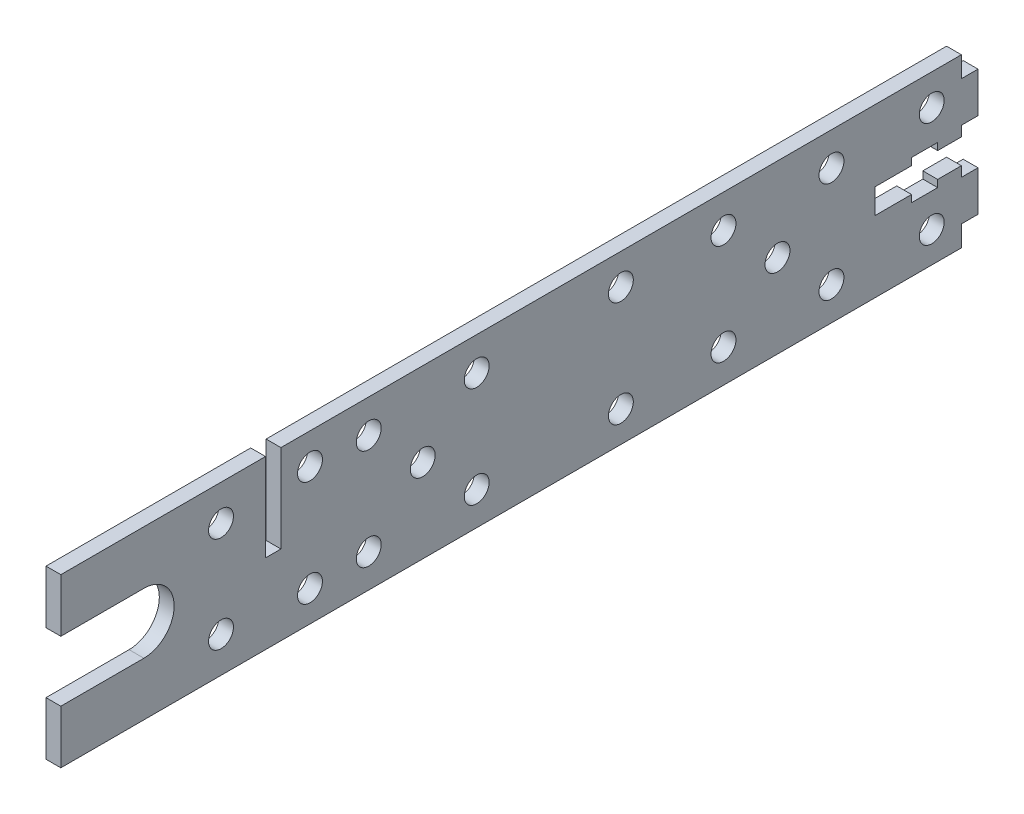
SolidWorks part; units mm, degrees
ref_plane "Front Plane" through (0, 0, 0) normal (0, 0, 1) x (1, 0, 0)
ref_plane "Top Plane" through (0, 0, 0) normal (0, 1, 0) x (1, 0, 0)
ref_plane "Right Plane" through (0, 0, 0) normal (1, 0, 0) x (0, 0, -1)
sketch "Sketch1" plane through (0, 0, 0) normal (1, 0, 0) x (0, 0, -1)
  line L0 (-98.171, 0) -> (98.171, 0) construction
  line L1 (-98.171, 17.907) -> (94.615, 17.907)
  line L2 (-98.171, 17.907) -> (-98.171, 6.477)
  line L3 (-98.171, -17.907) -> (94.615, -17.907)
  line L4 (98.171, 13.462) -> (98.171, 4.826)
  line L5 (94.615, 4.826) -> (94.615, 2.667)
  line L6 (94.615, -2.667) -> (94.615, -4.826)
  line L7 (94.615, 2.667) -> (89.535, 2.667)
  line L8 (94.615, 17.907) -> (94.615, 13.462)
  line L9 (94.615, -2.667) -> (89.535, -2.667)
  line L10 (76.073, 2.667) -> (76.073, -2.667)
  line L11 (86.741, 4.191) -> (86.741, -4.191) construction
  line L12 (-32.258, 10.795) -> (-9.144, 10.795) construction
  line L13 (83.947, 2.667) -> (76.073, 2.667)
  line L14 (89.535, 4.191) -> (83.947, 4.191)
  line L15 (89.535, 4.191) -> (89.535, 2.667)
  line L16 (89.535, -4.191) -> (83.947, -4.191)
  line L17 (83.947, 4.191) -> (83.947, 2.667)
  line L18 (66.802, 10.795) -> (43.688, 10.795) construction
  line L19 (66.802, -10.795) -> (43.688, -10.795) construction
  line L20 (83.947, -2.667) -> (76.073, -2.667)
  line L21 (89.535, -2.667) -> (89.535, -4.191)
  line L22 (83.947, -2.667) -> (83.947, -4.191)
  line L23 (98.171, -4.826) -> (98.171, -13.462)
  line L24 (98.171, 13.462) -> (94.615, 13.462)
  line L25 (98.171, 13.462) -> (98.171, 4.826)
  line L26 (98.171, 4.826) -> (94.615, 4.826)
  line L27 (-32.258, -10.795) -> (-9.144, -10.795) construction
  line L28 (98.171, 13.462) -> (94.615, 4.826) construction
  line L29 (98.171, 4.826) -> (94.615, 13.462) construction
  line L30 (-80.391, 6.477) -> (-98.171, 6.477)
  line L31 (98.171, -4.826) -> (94.615, -4.826)
  line L32 (-20.701, 10.795) -> (-20.701, -10.795) construction
  line L33 (98.171, -13.462) -> (94.615, -4.826) construction
  line L34 (98.171, -4.826) -> (94.615, -13.462) construction
  line L35 (98.171, -13.462) -> (94.615, -13.462)
  line L36 (-80.391, -6.477) -> (-98.171, -6.477)
  line L37 (-98.171, -6.477) -> (-98.171, -17.907)
  line L38 (94.615, -13.462) -> (94.615, -17.907)
  line L39 (55.245, 10.795) -> (55.245, -10.795) construction
  arc A0 (-80.391, -6.477) -> (-80.391, 6.477) centre (-80.391, 0) ccw
  circle A1 centre (-63.881, 10.287) radius 2.667
  circle A2 centre (-63.881, -10.287) radius 2.667
  circle A3 centre (-52.705, 0) radius 2.667
  circle A4 centre (-44.831, 11.303) radius 2.667
  circle A5 centre (21.717, 11.303) radius 2.667
  circle A6 centre (88.265, 11.303) radius 2.667
  circle A7 centre (88.265, -11.303) radius 2.667
  circle A8 centre (21.717, -11.303) radius 2.667
  circle A9 centre (-44.831, -11.303) radius 2.667
  circle A10 centre (-9.144, 10.795) radius 2.667
  circle A11 centre (-32.258, 10.795) radius 2.667
  circle A12 centre (66.802, 10.795) radius 2.667
  circle A13 centre (43.688, 10.795) radius 2.667
  circle A14 centre (43.688, -10.795) radius 2.667
  circle A15 centre (66.802, -10.795) radius 2.667
  circle A16 centre (-32.258, -10.795) radius 2.667
  circle A17 centre (-9.144, -10.795) radius 2.667
  circle A18 centre (-20.701, 0) radius 2.667
  circle A19 centre (55.245, 0) radius 2.667
  point P0 (0, 0)
  point P1 (86.741, 0)
  point P4 (0, 0)
  point P26 (96.393, 9.144)
  point P30 (96.393, -9.144)
  point P44 (76.073, 0)
  point P63 (55.245, 10.795)
  point P73 (-20.701, 10.795)
  dimension "D11" = 12.954
  dimension "D15" = 5.334
  dimension "D26" = 17.78
  dimension "D2" = 192.786
  dimension "D3" = 5.334
  dimension "D4" = 18.542
  dimension "D5" = 5.588
  dimension "D6" = 8.636
  dimension "D7" = 8.382
  dimension "D8" = 3.556
  dimension "D9" = 8.636
  dimension "D10" = 9.144
  dimension "D12" = 17.78
  dimension "D13" = 11.43
  dimension "D14" = 11.43
  dimension "D16" = 7.62
  dimension "D17" = 34.29
  dimension "D18" = 150.876
  dimension "D19" = 9.906
  dimension "D20" = 6.604
  dimension "D21" = 76.454
  dimension "D22" = 143.002
  dimension "D23" = 7.112
  dimension "D24" = 42.926
  dimension "D25" = 118.872
extrude "Boss-Extrude1" add sketch "Sketch1" along normal mid plane 3.175 contours A0 L36 L37 L3 L6 L9 L21 L16 L22 L20 L10 L13 L17 L14 L15 L7 L5 L26 L4 L24 L8 L1 L2 L30 A16 A14 A13 A12 A11 A10 A8 A2 A1 A3 A4 A5 | A3
sketch "Sketch2" plane through (1.5875, 0, 0) normal (1, 0, 0) x (0, 0, -1)
  line L0 (-98.171, 17.907) -> (94.615, 17.907) construction
  line L1 (-54.356, 17.907) -> (-51.054, 17.907)
  line L2 (-54.356, 17.907) -> (-54.356, -0.889)
  line L3 (-54.356, -0.889) -> (-51.054, -0.889)
  line L4 (-51.054, 17.907) -> (-51.054, -0.889)
  line L5 (-54.356, 17.907) -> (-51.054, -0.889) construction
  line L6 (-54.356, -0.889) -> (-51.054, 17.907) construction
  line L7 (98.171, -4.826) -> (98.171, -13.462) construction
  point P4 (-52.705, 8.509)
  point P9 (98.171, -9.144)
  dimension "D1" = 3.302
  dimension "D2" = 18.796
  dimension "D3" = 150.876
extrude "Cut-Extrude1" cut sketch "Sketch2" against normal through all
